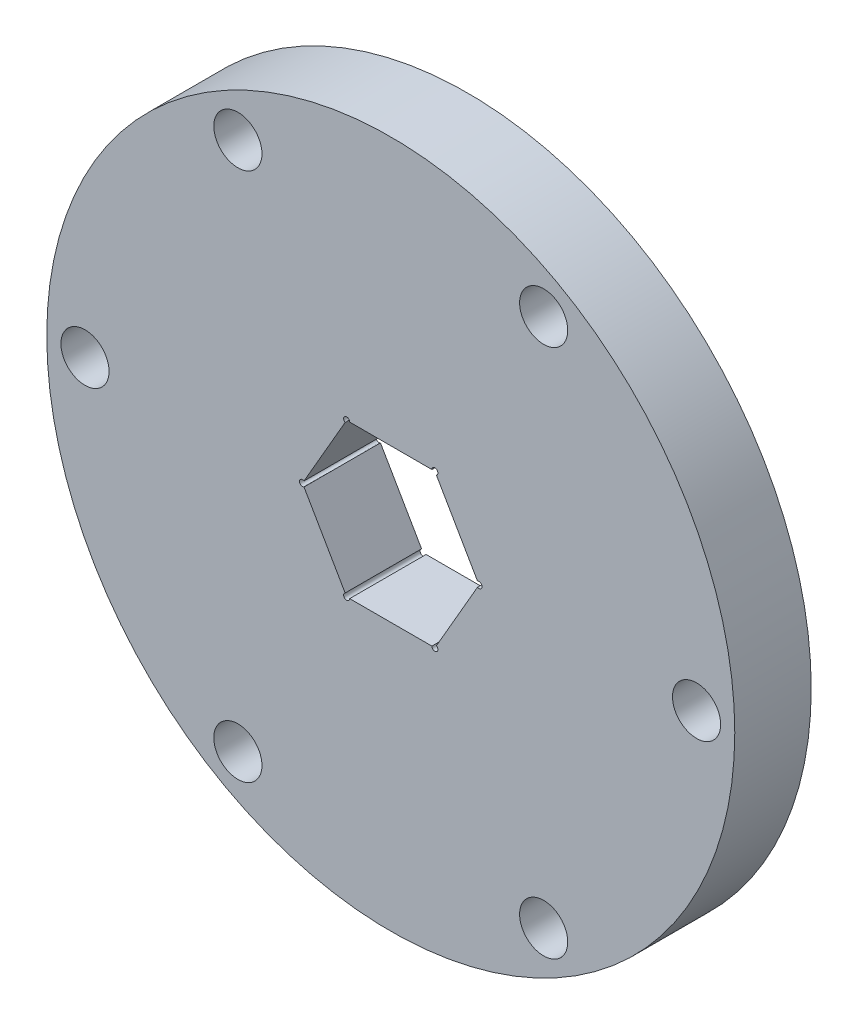
SolidWorks part; units mm, degrees
ref_plane "Front Plane" through (0, 0, 0) normal (0, 0, 1) x (1, 0, 0)
ref_plane "Top Plane" through (0, 0, 0) normal (0, 1, 0) x (1, 0, 0)
ref_plane "Right Plane" through (0, 0, 0) normal (1, 0, 0) x (0, 0, -1)
sketch "Sketch1" plane through (0, 0, 0) normal (0, 0, 1) x (1, 0, 0)
  circle A0 centre (0, 0) radius 28.575
  dimension "D1" = 57.15
extrude "Boss-Extrude1" add sketch "Sketch1" along normal blind 6.35
sketch "Sketch2" plane through (0, 0, 6.35) normal (0, 0, 1) x (1, 0, 0)
  circle A0 centre (0, 0) radius 14.2875
  dimension "D1" = 28.575
extrude "Boss-Extrude2" add sketch "Sketch2" along normal blind 12.7
sketch "Sketch3" plane through (0, 0, 19.05) normal (0, 0, 1) x (1, 0, 0)
  line L1 (7.3323, 0) -> (3.6662, 6.35)
  line L2 (3.6662, 6.35) -> (-3.6662, 6.35)
  line L3 (-3.6662, 6.35) -> (-7.3323, 0)
  line L4 (-7.3323, 0) -> (-3.6662, -6.35)
  line L5 (-3.6662, -6.35) -> (3.6662, -6.35)
  line L6 (3.6662, -6.35) -> (7.3323, 0)
  circle A0 centre (0, 0) radius 6.35 construction
  dimension "D1" = 12.7
extrude "Cut-Extrude1" cut sketch "Sketch3" against normal through all
sketch "Sketch4" plane through (0, 0, 6.35) normal (0, 0, 1) x (1, 0, 0)
  circle A0 centre (25.4, 0) radius 2
  circle A1 centre (0, 0) radius 28.575 construction
  circle A2 centre (12.7, -21.997) radius 2
  circle A3 centre (-12.7, -21.997) radius 2
  circle A4 centre (-25.4, 0) radius 2
  circle A5 centre (-12.7, 21.997) radius 2
  circle A6 centre (12.7, 21.997) radius 2
  point P19 (0, 0)
  dimension "D1" = 4
  dimension "D2" = 25.4
  dimension "D3" = 6
extrude "Cut-Extrude2" cut sketch "Sketch4" against normal through all
fillet "Fillet1" radius 1 6 edges at (0, 6.35, 19.05) (-5.4993, 3.175, 19.05) (-5.4993, -3.175, 19.05) (0, -6.35, 19.05) (5.4993, -3.175, 19.05) (5.4993, 3.175, 19.05)
sketch "Sketch5" plane through (0, 0, 19.05) normal (0, 0, 1) x (1, 0, 0)
  circle A0 centre (0, 0) radius 14.2875
extrude "Cut-Extrude4" cut sketch "Sketch5" against normal blind 12.7
sketch "Sketch7" plane through (0, 0, 6.35) normal (0, 0, 1) x (1, 0, 0)
  circle A0 centre (-3.6662, 6.35) radius 0.25
  circle A1 centre (3.6662, 6.35) radius 0.25
  circle A2 centre (7.3323, 0) radius 0.25
  circle A3 centre (3.6662, -6.35) radius 0.25
  circle A4 centre (-3.6662, -6.35) radius 0.25
  circle A5 centre (-7.3323, 0) radius 0.25
  point P16 (0, 0)
  dimension "D1" = 0.5
  dimension "D2" = 6
extrude "Cut-Extrude5" cut sketch "Sketch7" against normal blind 12.7
